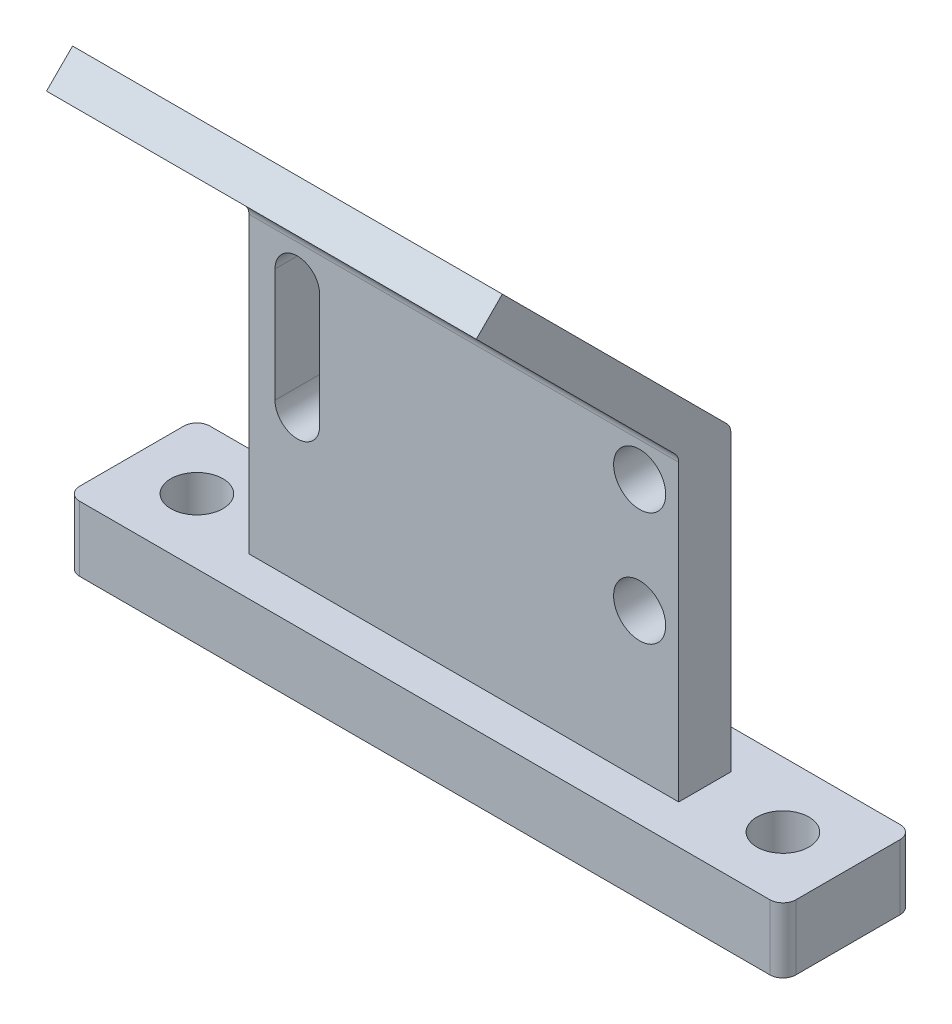
SolidWorks part; units mm, degrees
ref_plane "前视基准面" through (0, 0, 0) normal (0, 0, 1) x (1, 0, 0)
ref_plane "上视基准面" through (0, 0, 0) normal (0, 1, 0) x (1, 0, 0)
ref_plane "右视基准面" through (0, 0, 0) normal (1, 0, 0) x (0, 0, -1)
other "Configuration Table"
sketch "草图1" plane through (0, 0, 0) normal (0, 1, 0) x (1, 0, 0)
  line L0 (0.0338, 0) -> (0.0338, 2) construction
  line L2 (27.5338, -2.0074) -> (27.5338, 2.0025)
  line L4 (-27.4662, -1.9975) -> (-27.4662, 2.0025)
  line L5 (27.5338, -2.0074) -> (-27.4662, 2.0025) construction
  line L6 (27.5338, 2.0025) -> (-27.4662, -1.9975) construction
  line L7 (26.5338, -5) -> (18.5338, -5)
  line L8 (27.5338, -4) -> (27.5338, 4)
  line L9 (26.5338, 5) -> (18.5338, 5)
  line L10 (17.5338, -4) -> (17.5338, -3)
  line L11 (27.5338, -5) -> (17.5338, 5) construction
  line L12 (27.5338, 5) -> (17.5338, -5) construction
  line L13 (-26.4662, 5) -> (-18.4662, 5)
  line L14 (-17.4662, -4) -> (-17.4662, -3)
  line L15 (-26.4662, -5) -> (-18.4662, -5)
  line L16 (-27.4662, -4) -> (-27.4662, 4)
  line L17 (-17.4662, 3) -> (-17.4662, 4)
  line L18 (17.5338, 3) -> (17.5338, 4)
  line L19 (16.5338, -2) -> (-16.4662, -2)
  line L20 (16.5338, 2) -> (-16.4662, 2)
  arc A0 (18.5338, -5) -> (17.5338, -4) centre (18.5338, -4) cw
  arc A1 (26.5338, -5) -> (27.5338, -4) centre (26.5338, -4) ccw
  arc A2 (27.5338, 4) -> (26.5338, 5) centre (26.5338, 4) ccw
  arc A3 (18.5338, 5) -> (17.5338, 4) centre (18.5338, 4) ccw
  arc A4 (-18.4662, 5) -> (-17.4662, 4) centre (-18.4662, 4) cw
  arc A5 (-18.4662, -5) -> (-17.4662, -4) centre (-18.4662, -4) ccw
  arc A6 (-26.4662, -5) -> (-27.4662, -4) centre (-26.4662, -4) cw
  arc A7 (-27.4662, 4) -> (-26.4662, 5) centre (-26.4662, 4) cw
  arc A8 (-16.4662, -2) -> (-17.4662, -3) centre (-16.4662, -3) ccw
  arc A9 (-16.4662, 2) -> (-17.4662, 3) centre (-16.4662, 3) cw
  arc A10 (17.5338, 3) -> (16.5338, 2) centre (16.5338, 3) cw
  arc A11 (17.5338, -3) -> (16.5338, -2) centre (16.5338, -3) ccw
  point P0 (0, 0)
  point P6 (22.5338, 0)
  point P45 (-17.4662, 2)
  dimension "D6" = 1
  dimension "D7" = 1
  dimension "D1" = 55
  dimension "D2" = 4
  dimension "D3" = 5
  dimension "D4" = 10
  dimension "D5" = 10
extrude "凸台-拉伸2" add sketch "草图1" along normal blind 5 contours A11 L10 A0 L7 A1 L8 A2 L9 A3 L18 A10 L20 A9 L17 A4 L13 A7 L16 A6 L15 A5 L14 A8 L19
sketch "草图3" plane through (0, 0, 0) normal (0, -1, 0) x (1, 0, 0)
  line L0 (-16.4662, 2) -> (-16.4662, -2) construction
  line L1 (16.5338, 2) -> (16.5338, -2) construction
sketch "草图4" plane through (0, 5, 0) normal (0, 1, 0) x (1, 0, 0)
  line L0 (-16.4662, -2) -> (-16.4662, 2) construction
  line L1 (-16.4662, -2) -> (-16.4662, 2)
  line L2 (16.5338, -2) -> (16.5338, 2) construction
  line L3 (16.5338, -2) -> (-16.4662, -2) construction
  line L4 (16.5338, 2) -> (-16.4662, 2) construction
  line L5 (16.5338, -2) -> (16.5338, 2)
  line L6 (-16.4662, -2) -> (-16.4662, 2)
  line L7 (16.5338, -2) -> (-16.4662, -2)
  line L8 (16.5338, 2) -> (-16.4662, 2)
  line L10 (-16.4662, -2) -> (16.5338, -2)
  line L11 (-16.4662, -2) -> (-16.4662, 2)
  line L12 (-16.4662, -2) -> (16.5338, -2)
  line L13 (17.5338, -3) -> (17.5338, -4)
  line L14 (18.5338, -5) -> (26.5338, -5)
  line L15 (27.5338, -4) -> (27.5338, 4)
  line L16 (26.5338, 5) -> (18.5338, 5)
  line L17 (17.5338, 4) -> (17.5338, 3)
  line L18 (16.5338, 2) -> (-16.4662, 2)
  line L19 (-17.4662, 3) -> (-17.4662, 4)
  line L20 (-18.4662, 5) -> (-26.4662, 5)
  line L21 (-27.4662, 4) -> (-27.4662, -4)
  line L22 (-26.4662, -5) -> (-18.4662, -5)
  line L23 (-17.4662, -4) -> (-17.4662, -3)
  line L24 (-16.4662, -2) -> (16.5338, -2)
  line L25 (17.5338, -3) -> (17.5338, -4)
  line L26 (18.5338, -5) -> (26.5338, -5)
  line L27 (27.5338, -4) -> (27.5338, 4)
  line L28 (26.5338, 5) -> (18.5338, 5)
  line L29 (17.5338, 4) -> (17.5338, 3)
  line L30 (16.5338, 2) -> (-16.4662, 2)
  line L31 (-17.4662, 3) -> (-17.4662, 4)
  line L32 (-18.4662, 5) -> (-26.4662, 5)
  line L33 (-27.4662, 4) -> (-27.4662, -4)
  line L34 (-26.4662, -5) -> (-18.4662, -5)
  line L35 (-17.4662, -4) -> (-17.4662, -3)
  line L36 (-16.4662, 2) -> (16.5338, 2)
  line L37 (16.5338, -2) -> (16.5338, 2)
  arc A12 (17.5338, -3) -> (16.5338, -2) centre (16.5338, -3) ccw
  arc A13 (17.5338, -4) -> (18.5338, -5) centre (18.5338, -4) ccw
  arc A14 (26.5338, -5) -> (27.5338, -4) centre (26.5338, -4) ccw
  arc A15 (27.5338, 4) -> (26.5338, 5) centre (26.5338, 4) ccw
  arc A16 (18.5338, 5) -> (17.5338, 4) centre (18.5338, 4) ccw
  arc A17 (16.5338, 2) -> (17.5338, 3) centre (16.5338, 3) ccw
  arc A18 (-17.4662, 3) -> (-16.4662, 2) centre (-16.4662, 3) ccw
  arc A19 (-17.4662, 4) -> (-18.4662, 5) centre (-18.4662, 4) ccw
  arc A20 (-26.4662, 5) -> (-27.4662, 4) centre (-26.4662, 4) ccw
  arc A21 (-27.4662, -4) -> (-26.4662, -5) centre (-26.4662, -4) ccw
  arc A22 (-18.4662, -5) -> (-17.4662, -4) centre (-18.4662, -4) ccw
  arc A23 (-16.4662, -2) -> (-17.4662, -3) centre (-16.4662, -3) ccw
  arc A24 (17.5338, -3) -> (16.5338, -2) centre (16.5338, -3) ccw
  arc A25 (17.5338, -4) -> (18.5338, -5) centre (18.5338, -4) ccw
  arc A26 (26.5338, -5) -> (27.5338, -4) centre (26.5338, -4) ccw
  arc A27 (27.5338, 4) -> (26.5338, 5) centre (26.5338, 4) ccw
  arc A28 (18.5338, 5) -> (17.5338, 4) centre (18.5338, 4) ccw
  arc A29 (16.5338, 2) -> (17.5338, 3) centre (16.5338, 3) ccw
  arc A30 (-17.4662, 3) -> (-16.4662, 2) centre (-16.4662, 3) ccw
  arc A31 (-17.4662, 4) -> (-18.4662, 5) centre (-18.4662, 4) ccw
  arc A32 (-26.4662, 5) -> (-27.4662, 4) centre (-26.4662, 4) ccw
  arc A33 (-27.4662, -4) -> (-26.4662, -5) centre (-26.4662, -4) ccw
  arc A34 (-18.4662, -5) -> (-17.4662, -4) centre (-18.4662, -4) ccw
  arc A35 (-16.4662, -2) -> (-17.4662, -3) centre (-16.4662, -3) ccw
  point P0 (-16.4662, 2)
  dimension "D2" = 10
  dimension "D1" = 0
extrude "凸台-拉伸3" add sketch "草图4" along normal blind 23 contours L11 L10 L37 L36
sketch "草图5" plane through (-16.4662, 0, 0) normal (-1, 0, 0) x (0, 0, 1)
  line L0 (2.2929, 28.2929) -> (17.5445, 43.5445)
  line L1 (17.5445, 43.5445) -> (15.5445, 45.5445)
  line L2 (15.5445, 45.5445) -> (-1.7071, 28.2929)
  line L3 (2, 27.5858) -> (2, 5)
  line L4 (-2, 27.5858) -> (-2, 5)
  line L7 (-1.9102, 28) -> (-2, 28)
  line L8 (-2, 27.5858) -> (-2, 28)
  line L10 (-2, 5) -> (2, 5)
  line L11 (2, 5) -> (2, 28)
  line L12 (2, 28) -> (-2, 28)
  line L13 (-2, 28) -> (-2, 5)
  line L15 (2, 5) -> (2, 28)
  line L16 (2, 28) -> (-2, 28)
  line L17 (-2, 28) -> (-2, 5)
  arc A0 (2.2929, 28.2929) -> (2, 27.5858) centre (3, 27.5858) ccw
  arc A1 (-1.7071, 28.2929) -> (-2, 27.5858) centre (-1, 27.5858) ccw
  point P10 (2, 28)
  point P15 (-2, 28)
  line M5 (2, 5) -> (2, 28)
  line M6 (2, 28) -> (-2, 28)
  dimension "D1" = 1
  dimension "D2" = 1
  dimension "D3" = 0
extrude "凸台-拉伸4" add sketch "草图5" against normal blind 33 contours L2 A1 A0 L0 L1 M6 M5
sketch "草图11" plane through (0, 0, 2) normal (0, 0, 1) x (1, 0, 0)
  line L0 (-12.7501, 24.952) -> (-12.7501, 16.2196) construction
  line L1 (-11.034, 24.952) -> (-11.034, 16.2196)
  line L2 (-14.4662, 24.952) -> (-14.4662, 16.2196)
  line L3 (16.5338, 27.5858) -> (-16.4662, 27.5858) construction
  line L4 (-16.4662, 27.5858) -> (-16.4662, 5) construction
  line L5 (-12.7501, 24.952) -> (10.7248, 24.952) construction
  line L6 (-12.7501, 16.2196) -> (13.887, 16.2196) construction
  line L7 (16.5338, 27.5858) -> (16.5338, 5) construction
  arc A0 (-11.034, 24.952) -> (-14.4662, 24.952) centre (-12.7501, 24.952) ccw
  arc A1 (-14.4662, 16.2196) -> (-11.034, 16.2196) centre (-12.7501, 16.2196) ccw
  circle A2 centre (13.5338, 24.952) radius 2
  circle A3 centre (13.5338, 16.2196) radius 2
  point P2 (-12.7501, 20.5858)
  dimension "D1" = 7
  dimension "D2" = 2
  dimension "D3" = 3
  dimension "D4" = 3
sketch "草图13" plane through (0, 0, 2) normal (0, 0, 1) x (1, 0, 0)
extrude "切除-拉伸1" cut sketch "草图11" against normal blind 14 contours L2 A1 L1 A0 | A2 | A3
sketch "草图14" plane through (0, 0, 2) normal (0, 0, 1) x (1, 0, 0)
sketch "草图15" plane through (0, 0, 2) normal (0, 0, 1) x (1, 0, 0)
sketch "草图16" plane through (-16.4662, 0, 0) normal (-1, 0, 0) x (0, 0, 1)
  line L1 (-2, 28) -> (-2, 5) construction
  line L2 (-2, 27.5858) -> (-2, 28) construction
  line L3 (15.5445, 45.5445) -> (-1.7071, 28.2929) construction
  line L4 (17.5445, 43.5445) -> (15.5445, 45.5445) construction
  line L5 (2.2929, 28.2929) -> (17.5445, 43.5445) construction
  line L6 (2, 27.5858) -> (2, 5) construction
  line L7 (2, 5) -> (2, 28) construction
  line L8 (2, 28) -> (-2, 28) construction
  line L9 (-1.9102, 28) -> (-2, 28) construction
  line L11 (-2, 28) -> (-2, 27.5858)
  line L12 (-2, 27.5858) -> (-2, 28)
  line L13 (15.5445, 45.5445) -> (-1.7071, 28.2929)
  line L14 (17.5445, 43.5445) -> (15.5445, 45.5445)
  line L15 (2.2929, 28.2929) -> (17.5445, 43.5445)
  line L16 (2, 27.5858) -> (2, 5)
  line L17 (2, 5) -> (2, 28)
  line L18 (-1.9102, 28) -> (-2, 28)
  line L19 (-1.9102, 28) -> (-2, 28)
  arc A0 (-1.7071, 28.2929) -> (-2, 27.5858) centre (-1, 27.5858) ccw construction
  arc A1 (2.2929, 28.2929) -> (2, 27.5858) centre (3, 27.5858) ccw construction
  arc A2 (-1.9102, 28) -> (-2, 27.5858) centre (-1, 27.5858) ccw
  arc A3 (2.2929, 28.2929) -> (2, 27.5858) centre (3, 27.5858) ccw
  line M7 (-1.9102, 28) -> (-2, 28)
  line M8 (-2, 28) -> (-2, 5)
extrude "切除-拉伸2" cut sketch "草图16" against normal up to surface (33 mm away) contours A2 M7 M8 up to face at (16.5338, 26.5888, 3.5201)
sketch "草图17" plane through (0, 5, 0) normal (0, 1, 0) x (1, 0, 0)
  line L0 (-27.4662, -4) -> (-27.4662, 4) construction
  line L1 (-26.4662, -5) -> (-18.4662, -5) construction
  line L6 (16.5338, 2) -> (16.5338, -2)
  line L7 (17.5338, -3) -> (17.5338, -4)
  line L8 (18.5338, -5) -> (26.5338, -5)
  line L9 (27.5338, -4) -> (27.5338, 4)
  line L10 (26.5338, 5) -> (18.5338, 5)
  line L11 (17.5338, 4) -> (17.5338, 3)
  line L12 (16.5338, 2) -> (16.5338, -2)
  line L13 (17.5338, -3) -> (17.5338, -4)
  line L14 (18.5338, -5) -> (26.5338, -5)
  line L15 (27.5338, -4) -> (27.5338, 4)
  line L16 (26.5338, 5) -> (18.5338, 5)
  line L17 (17.5338, 4) -> (17.5338, 3)
  circle A0 centre (22.5338, 0) radius 2
  circle A1 centre (-22.4662, 0) radius 2
  arc A6 (17.5338, -3) -> (16.5338, -2) centre (16.5338, -3) ccw
  arc A7 (17.5338, -4) -> (18.5338, -5) centre (18.5338, -4) ccw
  arc A8 (26.5338, -5) -> (27.5338, -4) centre (26.5338, -4) ccw
  arc A9 (27.5338, 4) -> (26.5338, 5) centre (26.5338, 4) ccw
  arc A10 (18.5338, 5) -> (17.5338, 4) centre (18.5338, 4) ccw
  arc A11 (16.5338, 2) -> (17.5338, 3) centre (16.5338, 3) ccw
  arc A12 (17.5338, -3) -> (16.5338, -2) centre (16.5338, -3) ccw
  arc A13 (17.5338, -4) -> (18.5338, -5) centre (18.5338, -4) ccw
  arc A14 (26.5338, -5) -> (27.5338, -4) centre (26.5338, -4) ccw
  arc A15 (27.5338, 4) -> (26.5338, 5) centre (26.5338, 4) ccw
  arc A16 (18.5338, 5) -> (17.5338, 4) centre (18.5338, 4) ccw
  arc A17 (16.5338, 2) -> (17.5338, 3) centre (16.5338, 3) ccw
  dimension "D4" = 4
  dimension "D7" = 4
  dimension "D2" = 5
  dimension "D3" = 5
  dimension "D5" = 5
  dimension "D6" = 5
  dimension "D1" = 0
extrude "切除-拉伸3" cut sketch "草图17" against normal up to surface (5 mm away) contours A0 | A1 up to face at (0.0338, 0, 0)
sketch "草图19" plane through (0, 5, 0) normal (0, 1, 0) x (1, 0, 0)
  line L1 (-18.4662, 5) -> (18.5338, 5)
  line L2 (-18.4662, 5) -> (-18.4662, -5)
  line L3 (-18.4662, -5) -> (18.5338, -5)
  line L4 (18.5338, 5) -> (18.5338, -5)
extrude "凸台-拉伸5" add sketch "草图19" against normal blind 5
sketch "草图20" plane through (0, 0, 0) normal (0, -1, 0) x (1, 0, 0)
  line L0 (-27.4662, 4) -> (-27.4662, -4) construction
  line L1 (0, 0) -> (0, 20.5746) construction
  line L2 (26.5338, 5) -> (-26.4662, 5) construction
  circle A0 centre (-16.9662, 0) radius 2
  circle A1 centre (16.9662, 0) radius 2
  dimension "D2" = 4
  dimension "D1" = 10.5
  dimension "D3" = 5
